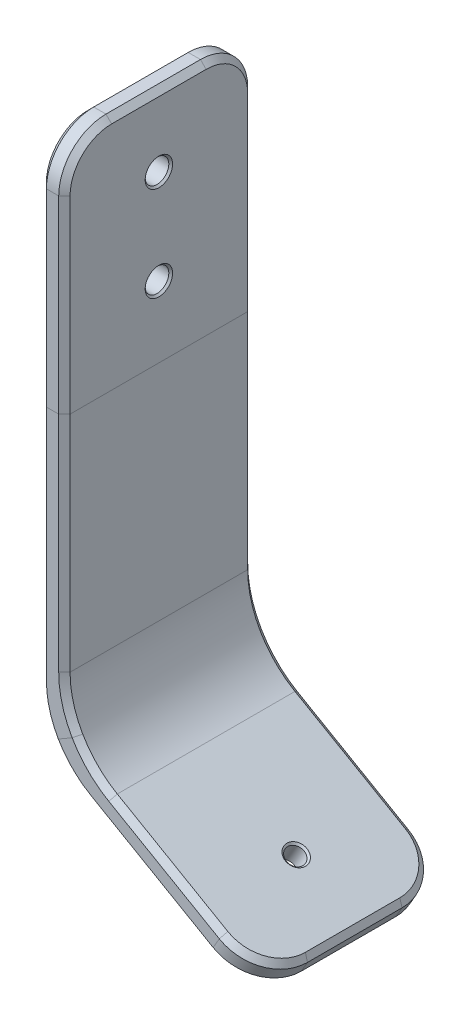
SolidWorks part; units mm, degrees
ref_plane "Front Plane" through (0, 0, 0) normal (0, 0, 1) x (1, 0, 0)
ref_plane "Top Plane" through (0, 0, 0) normal (0, 1, 0) x (1, 0, 0)
ref_plane "Right Plane" through (0, 0, 0) normal (1, 0, 0) x (0, 0, -1)
sketch "Sketch1" plane through (0, 0, 0) normal (0, 0, 1) x (1, 0, 0)
  line L0 (0, 0) -> (0, -31.75)
  line L1 (0, -31.75) -> (0, -70.0334)
  line L2 (0, -70.0334) -> (27.4963, -85.9084)
  dimension "D1" = 31.75
  dimension "D2" = 38.2834
  dimension "D3" = 180
  dimension "D4" = 120
  dimension "D5" = 31.75
sketch "Sketch2" plane through (0, 0, 0) normal (0, 1, 0) x (1, 0, 0)
  line L1 (-1.5875, -12.7) -> (1.5875, -12.7)
  line L2 (-1.5875, -12.7) -> (-1.5875, 12.7)
  line L3 (-1.5875, 12.7) -> (1.5875, 12.7)
  line L4 (1.5875, -12.7) -> (1.5875, 12.7)
  line L5 (-1.5875, -12.7) -> (1.5875, 12.7) construction
  line L6 (-1.5875, 12.7) -> (1.5875, -12.7) construction
  point P0 (0, 0)
  dimension "D1" = 3.175
  dimension "D2" = 25.4
sweep "Sweep1" add profiles "Sketch2" path "Sketch1"
hole_wizard "1/8 (0.125) Diameter Hole1" positions "Sketch3" profile "Sketch4" hole size "1/8" standard "ANSI Inch" end condition through all
sketch "Sketch3" plane through (1.5875, 0, 0) normal (1, 0, 0) x (0, 0, -1)
  line L0 (0, -22.225) -> (0, -31.75) construction
  line L1 (12.7, -31.75) -> (-12.7, -31.75) construction
  line L3 (0, -9.525) -> (0, 0) construction
  point P0 (0, -9.525)
  point P2 (0, -22.225)
  dimension "D1" = 12.7
sketch "Sketch4" plane through (1.5875, -9.525, 0) normal (0, 1, 0) x (0, 0, -1)
  line L0 (0, 0) -> (0, 3.175)
  line L1 (0, 3.175) -> (1.5875, 3.175)
  line L2 (1.5875, 3.175) -> (1.5875, 0)
  line L5 (1.5875, 0) -> (0, 0)
  line L11 (0, -6.35) -> (0, 107.95) construction
  dimension "Thru Hole Dia." = 3.175
  dimension "Thru Hole Depth" = 3.175
hole_wizard "3/32 (0.09375) Diameter Hole2" positions "Sketch5" profile "Sketch6" hole size "3/32" standard "ANSI Inch" end condition through all
sketch "Sketch5" plane through (-29.5316, -51.1502, 0) normal (0.5, 0.866, 0) x (0.866, -0.5, 0)
  line L1 (66.7667, -12.7) -> (66.7667, 12.7) construction
  point P0 (57.2417, 0)
  dimension "D1" = 9.525
sketch "Sketch6" plane through (20.0412, -79.7711, 0) normal (0, 0, 1) x (-0.866, 0.5, 0)
  line L0 (0, 0) -> (0, 17.32)
  line L1 (0, 17.32) -> (1.1906, 17.32)
  line L2 (1.1906, 17.32) -> (1.1906, 0)
  line L5 (1.1906, 0) -> (0, 0)
  line L11 (0, -6.35) -> (0, 107.95) construction
  dimension "Thru Hole Dia." = 2.3812
  dimension "Thru Hole Depth" = 17.32
fillet "Fillet1" radius 12.7 2 edges at (-1.5875, -70.95, 0) (1.5875, -69.1169, 0)
fillet "Fillet2" radius 6.35 4 edges at (27.4963, -85.9084, -12.7) (27.4963, -85.9084, 12.7) (0, 0, -12.7) (0, 0, 12.7)
chamfer "Chamfer3" distance 0.762 angle 45 32 edges at (-1.5875, -47.6838, -12.7) (-1.1548, -66.9046, -12.7) (2.1322, -72.5979, -12.7) (-1.5875, -19.05, -12.7) (12.9829, -79.3622, -12.7) (-1.5875, -1.8599, -10.8401) (25.0919, -86.3533, -10.8401) (-1.5875, 0, 0) (26.7026, -87.2832, 0) (-1.5875, -1.8599, 10.8401) (25.0919, -86.3533, 10.8401) (-1.5875, -19.05, 12.7) (12.9829, -79.3622, 12.7) (2.1322, -72.5979, 12.7) (-1.1548, -66.9046, 12.7) (-1.5875, -47.6838, 12.7) (1.5875, -46.7673, -12.7) (2.0202, -65.0715, -12.7) (5.3072, -70.7648, -12.7) (1.5875, -19.05, -12.7) (15.3641, -77.0708, -12.7) (1.5875, -1.8599, -10.8401) (26.6794, -83.6037, -10.8401) (1.5875, 0, 0) (28.2901, -84.5336, 0) (1.5875, -1.8599, 10.8401) (26.6794, -83.6037, 10.8401) (1.5875, -19.05, 12.7) (15.3641, -77.0708, 12.7) (5.3072, -70.7648, 12.7) (2.0202, -65.0715, 12.7) (1.5875, -46.7673, 12.7)
chamfer "Chamfer2" distance 0.254 angle 45 6 edges at (1.5875, -22.225, -1.5875) (-1.5875, -22.225, -1.5875) (1.5875, -9.525, -1.5875) (-1.5875, -9.525, -1.5875) (19.0101, -79.1758, 0) (17.4226, -81.9254, 0)
equation "\"D2@Sketch1\"=0.75+0.40625+0.350971"
